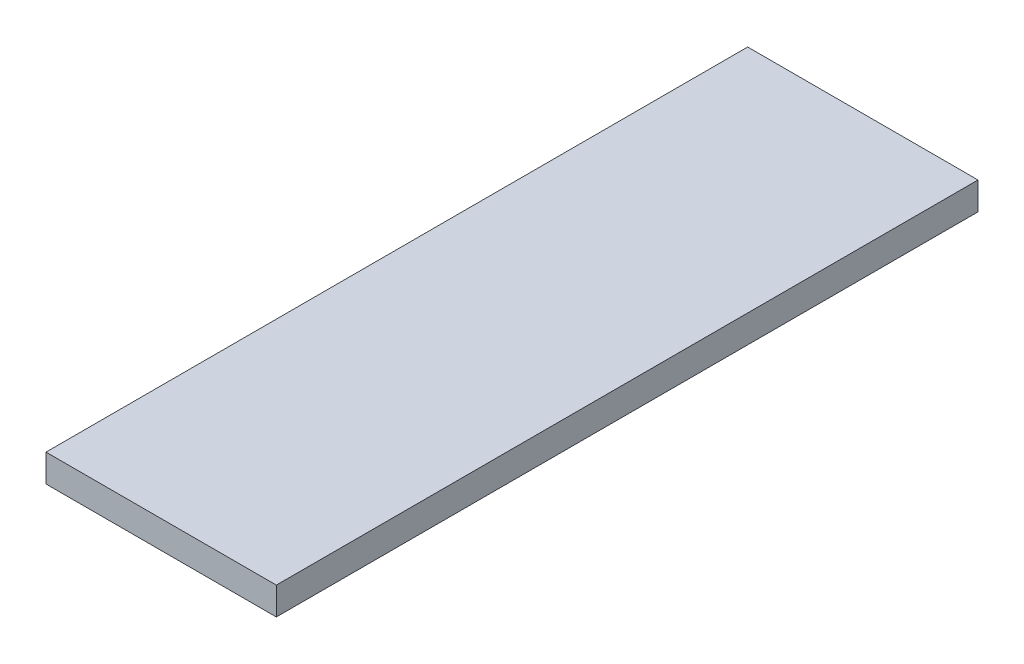
SolidWorks part; units mm, degrees
ref_plane "Front Plane" through (0, 0, 0) normal (0, 0, 1) x (1, 0, 0)
ref_plane "Top Plane" through (0, 0, 0) normal (0, 1, 0) x (1, 0, 0)
ref_plane "Right Plane" through (0, 0, 0) normal (1, 0, 0) x (0, 0, -1)
sketch "Sketch1" plane through (0, 0, 0) normal (0, 1, 0) x (1, 0, 0)
  line L1 (-6.25, 19.04) -> (6.25, 19.04)
  line L2 (-6.25, 19.04) -> (-6.25, -19.04)
  line L3 (-6.25, -19.04) -> (6.25, -19.04)
  line L4 (6.25, 19.04) -> (6.25, -19.04)
  line L5 (-6.25, 19.04) -> (6.25, -19.04) construction
  line L6 (-6.25, -19.04) -> (6.25, 19.04) construction
  point P0 (0, 0)
  dimension "D1" = 38.08
  dimension "D2" = 12.5
extrude "Boss-Extrude1" add sketch "Sketch1" along normal blind 1.5
